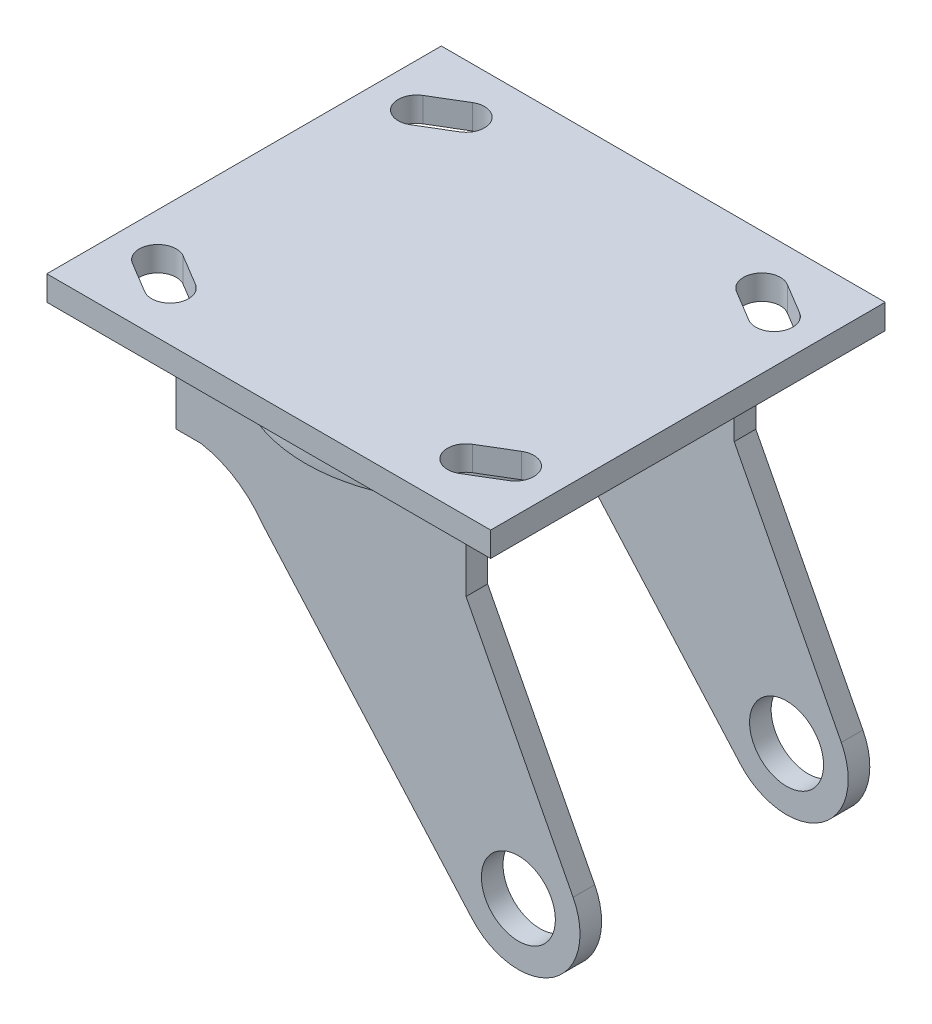
SolidWorks part; units mm, degrees
ref_plane "Plano frontal" through (0, 0, 0) normal (0, 0, 1) x (1, 0, 0)
ref_plane "Plano superior" through (0, 0, 0) normal (0, 1, 0) x (1, 0, 0)
ref_plane "Plano direito" through (0, 0, 0) normal (1, 0, 0) x (0, 0, -1)
ref_plane "Plano1" through (0, 0, 0) normal (0, 1, 0) x (1, 0, 0)
sketch "Esboço1" plane through (0, 0, 0) normal (0, 1, 0) x (1, 0, 0)
  line L0 (0, -50.8) -> (114.3, -50.8)
  line L1 (114.3, -50.8) -> (114.3, 50.8)
  line L2 (114.3, 50.8) -> (0, 50.8)
  line L3 (0, 50.8) -> (0, -50.8)
  line L4 (92.7997, 34.0162) -> (100.7372, 29.2537)
  line L5 (105.6378, 37.4213) -> (97.7003, 42.1838)
  line L6 (97.7003, -42.1838) -> (105.6378, -37.4213)
  line L7 (100.7372, -29.2537) -> (92.7997, -34.0162)
  line L8 (13.5628, 29.2537) -> (21.5003, 34.0162)
  line L9 (16.5997, 42.1838) -> (8.6622, 37.4213)
  line L10 (8.6622, -37.4213) -> (16.5997, -42.1838)
  line L11 (21.5003, -34.0162) -> (13.5628, -29.2537)
  arc A0 (97.7003, 42.1838) -> (92.7997, 34.0162) centre (95.25, 38.1) ccw
  arc A1 (100.7372, 29.2537) -> (105.6378, 37.4213) centre (103.1875, 33.3375) ccw
  arc A2 (92.7997, -34.0162) -> (97.7003, -42.1838) centre (95.25, -38.1) ccw
  arc A3 (105.6378, -37.4213) -> (100.7372, -29.2537) centre (103.1875, -33.3375) ccw
  arc A4 (8.6622, 37.4213) -> (13.5628, 29.2537) centre (11.1125, 33.3375) ccw
  arc A5 (21.5003, 34.0162) -> (16.5997, 42.1838) centre (19.05, 38.1) ccw
  arc A6 (13.5628, -29.2537) -> (8.6622, -37.4213) centre (11.1125, -33.3375) ccw
  arc A7 (16.5997, -42.1838) -> (21.5003, -34.0162) centre (19.05, -38.1) ccw
extrude "Ressalto-extrusão1" add sketch "Esboço1" along normal blind 6.35
ref_plane "Plano2" through (0, 0, 0) normal (0, 0, 1) x (1, 0, 0)
sketch "Esboço2" plane through (0, 0, 0) normal (0, 0, 1) x (1, 0, 0)
  line L0 (57.15, 0) -> (96.2121, 0)
  line L1 (98.425, -12.1906) -> (57.15, -12.1906)
  line L2 (57.15, -12.1906) -> (57.15, 0)
  line L3 (57.15, -12.1906) -> (57.15, 0) construction
  arc A0 (96.2121, 0) -> (98.425, -12.1906) centre (68.9291, -11.2488) cw
revolve "Revolução1" add sketch "Esboço2" angle 360 about L3
ref_plane "Plano3" through (0, 0, 0) normal (1, 0, 0) x (0, 0, -1)
sketch "Esboço3" plane through (0, 0, 0) normal (1, 0, 0) x (0, 0, -1)
  line L0 (-37.3126, -101.6) -> (37.3126, -101.6)
  line L1 (37.3126, -101.6) -> (37.3126, -11.9126)
  line L2 (37.3126, -11.9126) -> (-37.3126, -11.9126)
  line L3 (-37.3126, -11.9126) -> (-37.3126, -101.6)
extrude "Ressalto-extrusão2" add sketch "Esboço3" along normal blind 129.54
ref_plane "Plano4" through (0, 0, 0) normal (1, 0, 0) x (0, 0, -1)
sketch "Esboço4" plane through (0, 0, 0) normal (1, 0, 0) x (0, 0, -1)
  line L0 (-31.75, -27.324) -> (-31.75, -101.6)
  line L1 (-31.75, -101.6) -> (31.75, -101.6)
  line L2 (31.75, -101.6) -> (31.75, -27.324)
  line L3 (20.0604, -11.9126) -> (-20.0604, -11.9126)
  arc A0 (31.75, -27.324) -> (20.0604, -11.9126) centre (15.7461, -27.324) ccw
  arc A1 (-20.0604, -11.9126) -> (-31.75, -27.324) centre (-15.7461, -27.324) ccw
extrude "Corte-extrusão1" cut sketch "Esboço4" along normal blind 129.54
ref_plane "Plano5" through (0, 0, 37.3126) normal (0, 0, 1) x (1, 0, 0)
sketch "Esboço5" plane through (0, 0, 37.3126) normal (0, 0, 1) x (1, 0, 0)
  line L0 (0, -11.9126) -> (0, -113.5126)
  line L1 (0, -113.5126) -> (129.54, -113.5126)
  line L2 (129.54, -113.5126) -> (129.54, -11.9126)
  line L3 (129.54, -11.9126) -> (94.4727, -11.9126)
  line L4 (94.4727, -11.9126) -> (94.4727, -25.122)
  line L5 (94.4727, -25.122) -> (122.05, -78.4309)
  line L6 (96.059, -96.2426) -> (41.9795, -35.1016)
  line L7 (26.1773, -25.122) -> (19.8273, -25.122)
  line L8 (19.8273, -25.122) -> (19.8273, -11.9126)
  line L9 (19.8273, -11.9126) -> (0, -11.9126)
  arc A0 (122.05, -78.4309) -> (96.059, -96.2426) centre (107.95, -85.725) cw
  arc A1 (41.9795, -35.1016) -> (26.1773, -25.122) centre (22.0381, -49.1769) ccw
extrude "Corte-extrusão2" cut sketch "Esboço5" against normal blind 17.78
ref_plane "Plano6" through (0, 0, -37.3126) normal (0, 0, 1) x (1, 0, 0)
sketch "Esboço6" plane through (0, 0, -37.3126) normal (0, 0, 1) x (1, 0, 0)
  line L0 (0, -11.9126) -> (0, -113.5126)
  line L1 (0, -113.5126) -> (129.54, -113.5126)
  line L2 (129.54, -113.5126) -> (129.54, -11.9126)
  line L3 (129.54, -11.9126) -> (94.4727, -11.9126)
  line L4 (94.4727, -11.9126) -> (94.4727, -25.122)
  line L5 (94.4727, -25.122) -> (122.05, -78.4309)
  line L6 (96.059, -96.2426) -> (41.9795, -35.1016)
  line L7 (26.1773, -25.122) -> (19.8273, -25.122)
  line L8 (19.8273, -25.122) -> (19.8273, -11.9126)
  line L9 (19.8273, -11.9126) -> (0, -11.9126)
  arc A0 (122.05, -78.4309) -> (96.059, -96.2426) centre (107.95, -85.725) cw
  arc A1 (41.9795, -35.1016) -> (26.1773, -25.122) centre (22.0381, -49.1769) ccw
extrude "Corte-extrusão3" cut sketch "Esboço6" along normal blind 17.78
ref_plane "Plano7" through (0, 0, 37.3126) normal (0, 0, 1) x (1, 0, 0)
sketch "Esboço7" plane through (0, 0, 37.3126) normal (0, 0, 1) x (1, 0, 0)
  circle A0 centre (107.95, -85.725) radius 9.525
extrude "Corte-extrusão4" cut sketch "Esboço7" against normal blind 5.5626
ref_plane "Plano8" through (0, 0, -37.3126) normal (0, 0, 1) x (1, 0, 0)
sketch "Esboço8" plane through (0, 0, -37.3126) normal (0, 0, 1) x (1, 0, 0)
  circle A0 centre (107.95, -85.725) radius 9.525
extrude "Corte-extrusão5" cut sketch "Esboço8" along normal blind 5.5626
ref_plane "Plano9" through (0, 0, 0) normal (0, 0, 1) x (1, 0, 0)
sketch "Esboço9" plane through (0, 0, 0) normal (0, 0, 1) x (1, 0, 0)
  line L0 (79.375, -65.0875) -> (150.0006, -65.0875)
  line L1 (175.0128, -44.1091) -> (110.4951, -17.4625)
  line L2 (110.4951, -17.4625) -> (79.375, -17.4625)
  line L3 (69.85, -26.9875) -> (69.85, -55.5625)
  arc A0 (69.85, -55.5625) -> (79.375, -65.0875) centre (79.375, -55.5625) ccw
  arc A1 (150.0006, -65.0875) -> (175.0128, -44.1091) centre (150.0006, -39.6875) ccw
  arc A2 (79.375, -17.4625) -> (69.85, -26.9875) centre (79.375, -26.9875) ccw
extrude "Corte-extrusão6" cut sketch "Esboço9" against normal blind 31.75 and the other way blind 31.75
